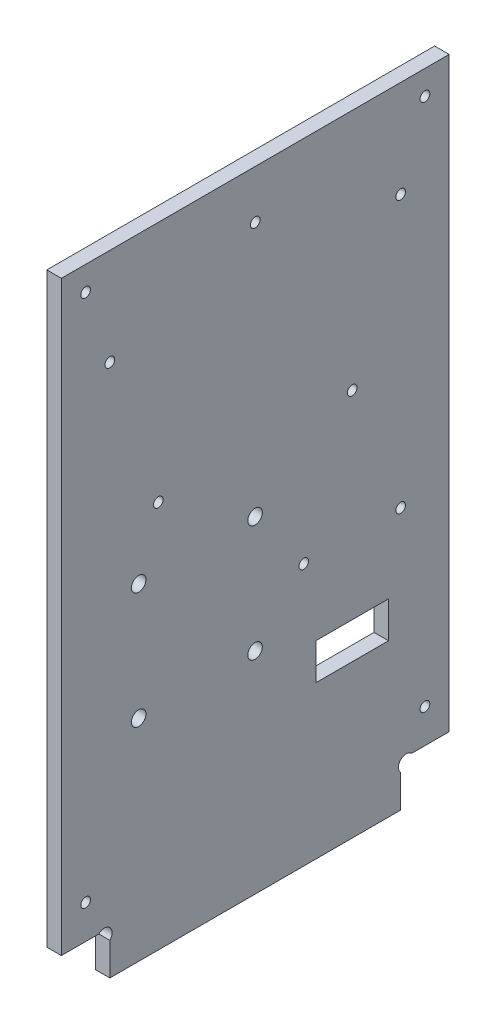
SolidWorks part; units mm, degrees
ref_plane "Plan de face" through (0, 0, 0) normal (0, 0, 1) x (1, 0, 0)
ref_plane "Plan de dessus" through (0, 0, 0) normal (0, 1, 0) x (1, 0, 0)
ref_plane "Plan de droite" through (0, 0, 0) normal (1, 0, 0) x (0, 0, -1)
sketch "Esquisse1" plane through (0, 0, 0) normal (1, 0, 0) x (0, 0, -1)
  line L8 (10, 6.7373) -> (10, 0)
  line L9 (70, 6.7373) -> (70, 0)
  line L10 (7.7373, 9) -> (0, 9)
  line L11 (10, 0) -> (70, 0)
  line L12 (72.2627, 9) -> (80, 9)
  line L13 (0, 9) -> (0, 130)
  line L14 (0, 130) -> (80, 130)
  line L15 (80, 130) -> (80, 9)
  arc A0 (10, 6.7373) -> (7.7373, 9) centre (8.8686, 7.8686) ccw
  arc A1 (70, 6.7373) -> (72.2627, 9) centre (71.1314, 7.8686) cw
  dimension "D7" = 1.1314
  dimension "D6" = 1.6
  dimension "D1" = 9
  dimension "D2" = 10
  dimension "D3" = 10
  dimension "D4" = 80
  dimension "D5" = 130
  dimension "D8" = 1.1314
  dimension "D9" = 1.1314
  dimension "D10" = 1.1314
extrude "Extrusion1" add sketch "Esquisse1" along normal blind 3
sketch "Esquisse2" plane through (3, 0, 0) normal (1, 0, 0) x (0, 0, -1)
  line L0 (0, 9) -> (7.7373, 9) construction
  line L1 (0, 130) -> (0, 9) construction
  line L2 (80, 9) -> (80, 130) construction
  line L3 (72.2627, 9) -> (80, 9) construction
  line L4 (80, 130) -> (0, 130) construction
  circle A0 centre (60, 80) radius 1
  circle A1 centre (10, 110) radius 1
  circle A2 centre (20, 80) radius 1
  circle A3 centre (70, 110) radius 1
  circle A4 centre (15.95, 67.45) radius 1.5
  circle A5 centre (15.95, 43.45) radius 1.5
  circle A6 centre (39.95, 43.45) radius 1.5
  circle A7 centre (39.95, 67.45) radius 1.5
  circle A8 centre (40, 120) radius 1
  circle A9 centre (70, 54) radius 1
  circle A10 centre (50, 54) radius 1
  dimension "D5" = 15.95
  dimension "D7" = 10
  dimension "D9" = 10
  dimension "D4" = 3
  dimension "D6" = 2
  dimension "D1" = 58.45
  dimension "D2" = 24
  dimension "D3" = 24
  dimension "D8" = 40
  dimension "D10" = 30
  dimension "D11" = 10
  dimension "D12" = 20
  dimension "D13" = 10
  dimension "D14" = 10
  dimension "D15" = 10
  dimension "D16" = 20
  dimension "D17" = 45
extrude "Enlèv. mat.-Extru.1" cut sketch "Esquisse2" against normal through all
sketch "Esquisse3" plane through (0, 0, 0) normal (-1, 0, 0) x (0, 0, 1)
  line L1 (-67.5, 39) -> (-52.5, 39)
  line L2 (-67.5, 39) -> (-67.5, 31.5)
  line L3 (-67.5, 31.5) -> (-52.5, 31.5)
  line L4 (-52.5, 39) -> (-52.5, 31.5)
  circle A0 centre (-70, 54) radius 1 construction
  circle A1 centre (-50, 54) radius 1 construction
  dimension "D4" = 2.5
  dimension "D1" = 15
  dimension "D2" = 7.5
  dimension "D3" = 15
  dimension "D5" = 2.5
extrude "Enlèv. mat.-Extru.2" cut sketch "Esquisse3" against normal through all
sketch "Esquisse4" plane through (3, 0, 0) normal (1, 0, 0) x (0, 0, -1)
  line L0 (80, 130) -> (0, 130) construction
  line L1 (0, 130) -> (0, 9) construction
  line L2 (80, 9) -> (80, 130) construction
  line L3 (0, 9) -> (7.7373, 9) construction
  circle A0 centre (5, 125) radius 1
  circle A1 centre (75, 125) radius 1
  circle A2 centre (75, 16) radius 1
  circle A3 centre (5, 16) radius 1
  dimension "D1" = 2
  dimension "D2" = 5
  dimension "D3" = 5
  dimension "D4" = 5
  dimension "D5" = 7
extrude "Enlèv. mat.-Extru.3" cut sketch "Esquisse4" against normal through all
